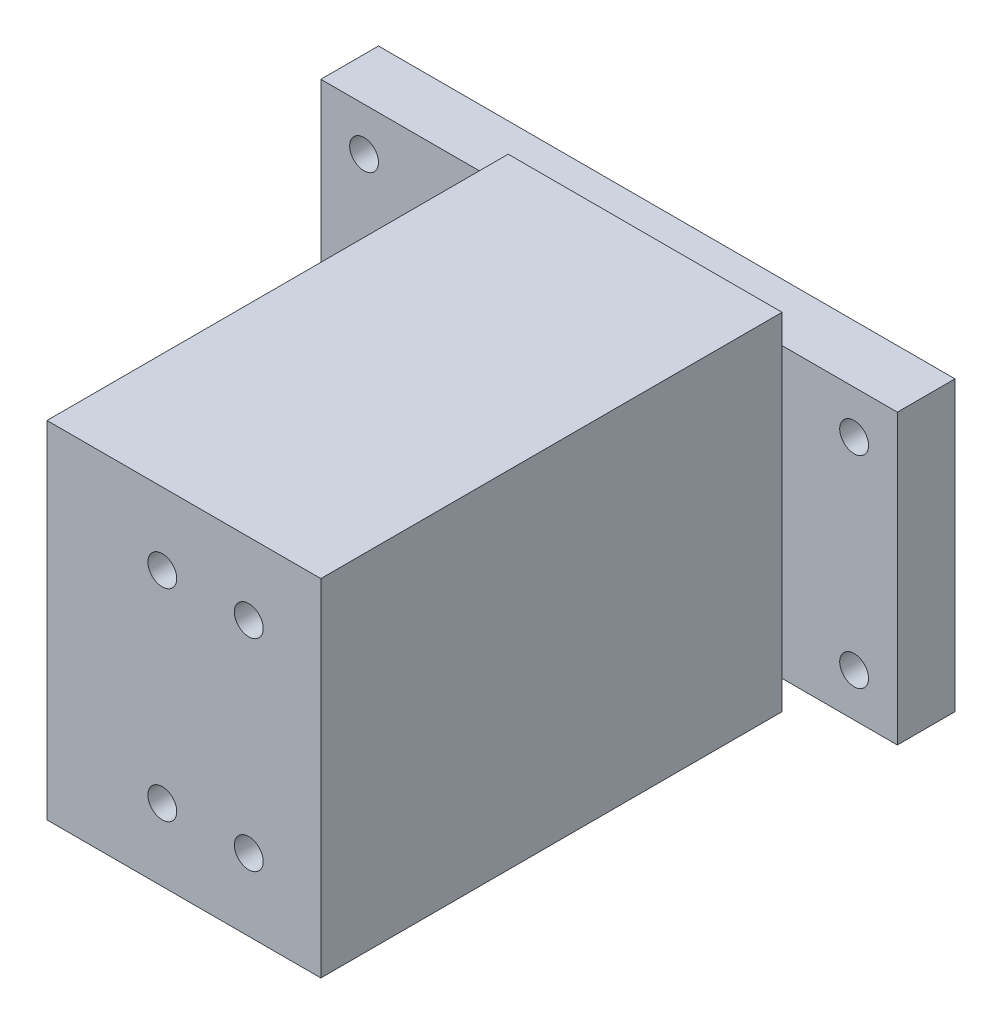
SolidWorks part; units mm, degrees
material "5052-H32"
ref_plane "Front Plane" through (0, 0, 0) normal (0, 0, 1) x (1, 0, 0)
ref_plane "Top Plane" through (0, 0, 0) normal (0, 1, 0) x (1, 0, 0)
ref_plane "Right Plane" through (0, 0, 0) normal (1, 0, 0) x (0, 0, -1)
sketch "Sketch1" plane through (0, 0, 0) normal (0, 0, 1) x (1, 0, 0)
  line L1 (-50, 25) -> (50, 25)
  line L2 (-50, 25) -> (-50, -25)
  line L3 (-50, -25) -> (50, -25)
  line L4 (50, 25) -> (50, -25)
  line L5 (-50, 25) -> (50, -25) construction
  line L6 (-50, -25) -> (50, 25) construction
  circle A0 centre (-42.5, 17.5) radius 2.5
  circle A1 centre (42.5, 17.5) radius 2.5
  circle A2 centre (42.5, -17.5) radius 2.5
  circle A3 centre (-42.5, -17.5) radius 2.5
  point P0 (0, 0)
  dimension "D3" = 5
  dimension "D1" = 100
  dimension "D2" = 50
  dimension "D4" = 7.5
  dimension "D5" = 7.5
  dimension "D6" = 85
  dimension "D7" = 35
extrude "Boss-Extrude1" add sketch "Sketch1" along normal blind 10
sketch "Sketch2" plane through (0, 0, 10) normal (0, 0, 1) x (1, 0, 0)
  line L1 (-17.5, 30) -> (30, 30)
  line L2 (-17.5, 30) -> (-17.5, -30)
  line L3 (-17.5, -30) -> (30, -30)
  line L4 (30, 30) -> (30, -30)
  line L5 (50, -25) -> (50, 25) construction
  line L6 (50, 25) -> (-50, 25) construction
  point P0 (0, 0)
  dimension "D1" = 60
  dimension "D2" = 47.5
  dimension "D3" = 20
  dimension "D4" = 5
extrude "Boss-Extrude2" add sketch "Sketch2" along normal blind 80
sketch "Sketch3" plane through (0, 0, 90) normal (0, 0, 1) x (1, 0, 0)
  line L0 (30, -30) -> (30, 30) construction
  line L1 (-17.5, -30) -> (30, -30) construction
  circle A0 centre (17.5, 17.5) radius 2.5
  circle A1 centre (2.5, 17.5) radius 2.5
  circle A2 centre (2.5, -17.5) radius 2.5
  circle A3 centre (17.5, -17.5) radius 2.5
  dimension "D1" = 35
  dimension "D5" = 5
  dimension "D2" = 15
  dimension "D3" = 12.5
  dimension "D4" = 12.5
extrude "Cut-Extrude1" cut sketch "Sketch3" against normal blind 10
sketch "Sketch9" plane through (-17.5, 0, 0) normal (-1, 0, 0) x (0, 0, 1)
  line L0 (90, 30) -> (90, -30) construction
  line L1 (90, 30) -> (10, 30) construction
  circle A0 centre (77.5, 15) radius 2.5
  circle A1 centre (42.5, 15) radius 2.5
  circle A2 centre (42.5, -20) radius 2.5
  circle A3 centre (77.5, -20) radius 2.5
  dimension "D1" = 5
  dimension "D2" = 35
  dimension "D3" = 35
  dimension "D4" = 12.5
  dimension "D5" = 15
extrude "Cut-Extrude18" cut sketch "Sketch9" against normal blind 10 contours A0 | A2 | A3 | A1
